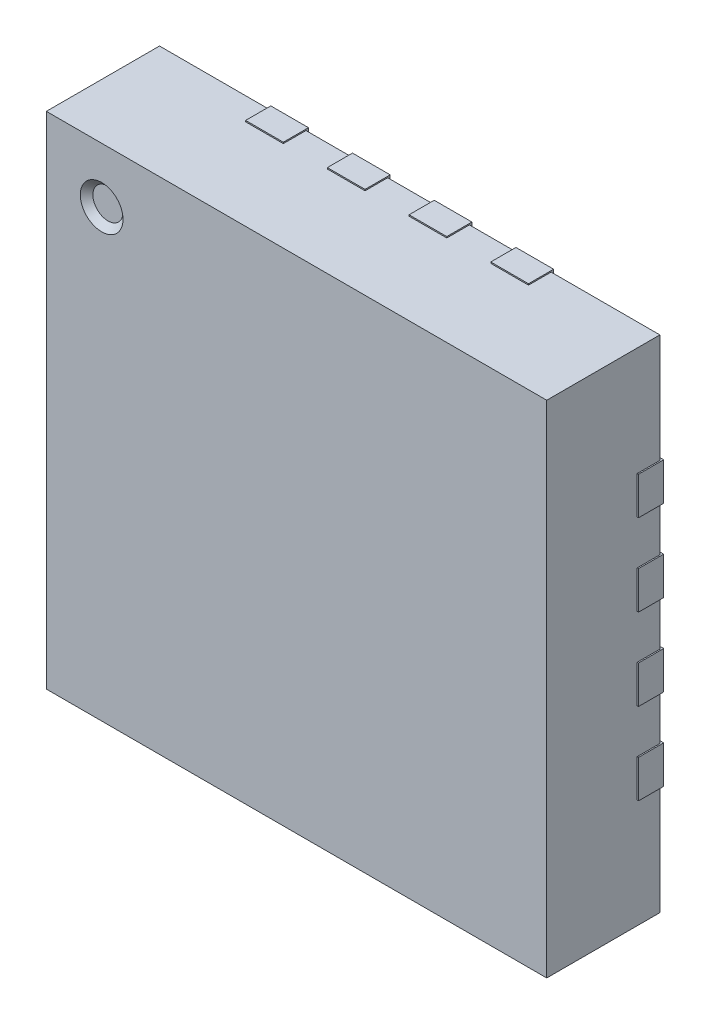
SolidWorks part; units mm, degrees
ref_plane "Спереди" through (0, 0, 0) normal (0, 0, 1) x (1, 0, 0)
ref_plane "Сверху" through (0, 0, 0) normal (0, 1, 0) x (1, 0, 0)
ref_plane "Справа" through (0, 0, 0) normal (1, 0, 0) x (0, 0, -1)
sketch "Эскиз1" plane through (0, 0, 0) normal (0, 0, 1) x (1, 0, 0)
  line L1 (-1.99, 1.99) -> (1.99, 1.99)
  line L2 (-1.99, 1.99) -> (-1.99, -1.99)
  line L3 (-1.99, -1.99) -> (1.99, -1.99)
  line L4 (1.99, 1.99) -> (1.99, -1.99)
extrude "Вытянуть1" add sketch "Эскиз1" along normal blind 0.9 from offset 0.02
sketch "Эскиз2" plane through (0, 0, 0.92) normal (0, 0, 1) x (1, 0, 0)
  circle A0 centre (-1.55, 1.55) radius 0.17
extrude "Вытянуть2" cut sketch "Эскиз2" against normal blind 0.05 draft 45
sketch "Эскиз3" plane through (0, 0, 0) normal (0, 0, 1) x (1, 0, 0)
  line L0 (-2, -0.175) -> (-2, -0.475)
  line L1 (-2, -0.175) -> (-1.6, -0.175)
  line L2 (-1.6, -0.175) -> (-1.6, -0.475)
  line L3 (-2, -0.475) -> (-1.6, -0.475)
  line L4 (-1.6, -1.125) -> (-1.6, -0.825)
  line L5 (-1.6, -1.125) -> (-2, -1.125)
  line L6 (-2, -1.125) -> (-2, -0.825)
  line L7 (-1.6, -0.825) -> (-2, -0.825)
  line L8 (-1.6, 0.825) -> (-2, 0.825)
  line L9 (-2, 1.125) -> (-2, 0.825)
  line L10 (-1.6, 1.125) -> (-2, 1.125)
  line L11 (-1.6, 1.125) -> (-1.6, 0.825)
  line L12 (-1.6, 0.175) -> (-2, 0.175)
  line L13 (-2, 0.475) -> (-2, 0.175)
  line L14 (-1.6, 0.475) -> (-2, 0.475)
  line L15 (-1.6, 0.475) -> (-1.6, 0.175)
  line L16 (-0.175, 2) -> (-0.475, 2)
  line L17 (-0.175, 2) -> (-0.175, 1.6)
  line L18 (-0.175, 1.6) -> (-0.475, 1.6)
  line L19 (-0.475, 2) -> (-0.475, 1.6)
  line L20 (-1.125, 1.6) -> (-0.825, 1.6)
  line L21 (-1.125, 1.6) -> (-1.125, 2)
  line L22 (-1.125, 2) -> (-0.825, 2)
  line L23 (-0.825, 1.6) -> (-0.825, 2)
  line L24 (0.825, 1.6) -> (0.825, 2)
  line L25 (1.125, 2) -> (0.825, 2)
  line L26 (1.125, 1.6) -> (1.125, 2)
  line L27 (1.125, 1.6) -> (0.825, 1.6)
  line L28 (0.175, 1.6) -> (0.175, 2)
  line L29 (0.475, 2) -> (0.175, 2)
  line L30 (0.475, 1.6) -> (0.475, 2)
  line L31 (0.475, 1.6) -> (0.175, 1.6)
  line L32 (2, 0.175) -> (2, 0.475)
  line L33 (2, 0.175) -> (1.6, 0.175)
  line L34 (1.6, 0.175) -> (1.6, 0.475)
  line L35 (2, 0.475) -> (1.6, 0.475)
  line L36 (1.6, 1.125) -> (1.6, 0.825)
  line L37 (1.6, 1.125) -> (2, 1.125)
  line L38 (2, 1.125) -> (2, 0.825)
  line L39 (1.6, 0.825) -> (2, 0.825)
  line L40 (1.6, -0.825) -> (2, -0.825)
  line L41 (2, -1.125) -> (2, -0.825)
  line L42 (1.6, -1.125) -> (2, -1.125)
  line L43 (1.6, -1.125) -> (1.6, -0.825)
  line L44 (1.6, -0.175) -> (2, -0.175)
  line L45 (2, -0.475) -> (2, -0.175)
  line L46 (1.6, -0.475) -> (2, -0.475)
  line L47 (1.6, -0.475) -> (1.6, -0.175)
  line L68 (0.175, -2) -> (0.475, -2)
  line L69 (0.175, -2) -> (0.175, -1.6)
  line L70 (0.175, -1.6) -> (0.475, -1.6)
  line L71 (0.475, -2) -> (0.475, -1.6)
  line L72 (1.125, -1.6) -> (0.825, -1.6)
  line L73 (1.125, -1.6) -> (1.125, -2)
  line L74 (1.125, -2) -> (0.825, -2)
  line L75 (0.825, -1.6) -> (0.825, -2)
  line L88 (-0.825, -1.6) -> (-0.825, -2)
  line L89 (-1.125, -2) -> (-0.825, -2)
  line L90 (-1.125, -1.6) -> (-1.125, -2)
  line L91 (-1.125, -1.6) -> (-0.825, -1.6)
  line L92 (-0.175, -1.6) -> (-0.175, -2)
  line L93 (-0.475, -2) -> (-0.175, -2)
  line L94 (-0.475, -1.6) -> (-0.475, -2)
  line L95 (-0.475, -1.6) -> (-0.175, -1.6)
extrude "Вытянуть3" add sketch "Эскиз3" along normal blind 0.2
